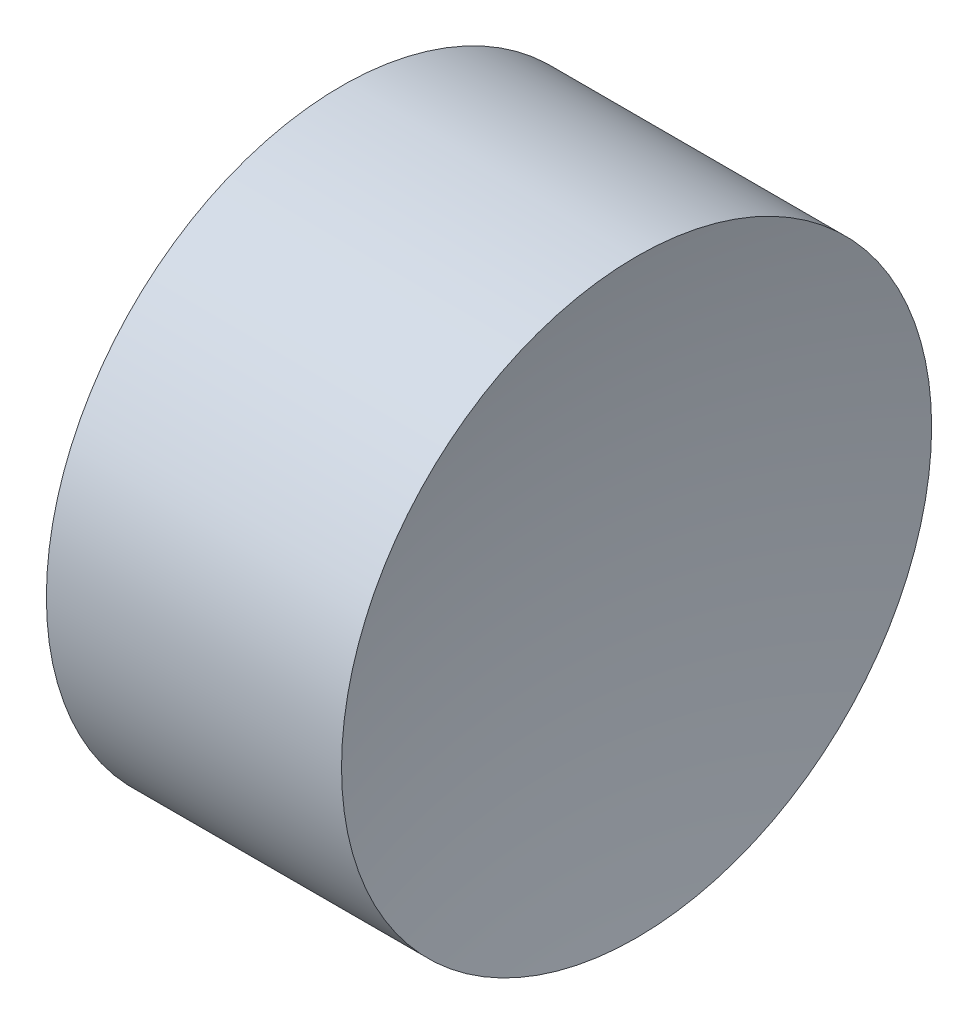
SolidWorks part; units mm, degrees
ref_plane "前视基准面" through (0, 0, 0) normal (0, 0, 1) x (1, 0, 0)
ref_plane "上视基准面" through (0, 0, 0) normal (0, 1, 0) x (1, 0, 0)
ref_plane "右视基准面" through (0, 0, 0) normal (1, 0, 0) x (0, 0, -1)
sketch "草图1" plane through (0, 0, 0) normal (0, 0, 1) x (1, 0, 0)
  line L0 (10.5782, 6.5156) -> (13.4181, 6.5156) construction
  line L1 (11.0806, 6.5156) -> (11.0806, 8.5156)
  line L2 (11.0806, 8.5156) -> (13.0814, 8.5156)
  line L3 (12.8606, 6.5156) -> (11.0806, 6.5156)
  arc A0 (13.0814, 8.5156) -> (12.8606, 6.5156) centre (22.0306, 6.5156) ccw
revolve "旋转1" add sketch "草图1" angle 360 about L0
